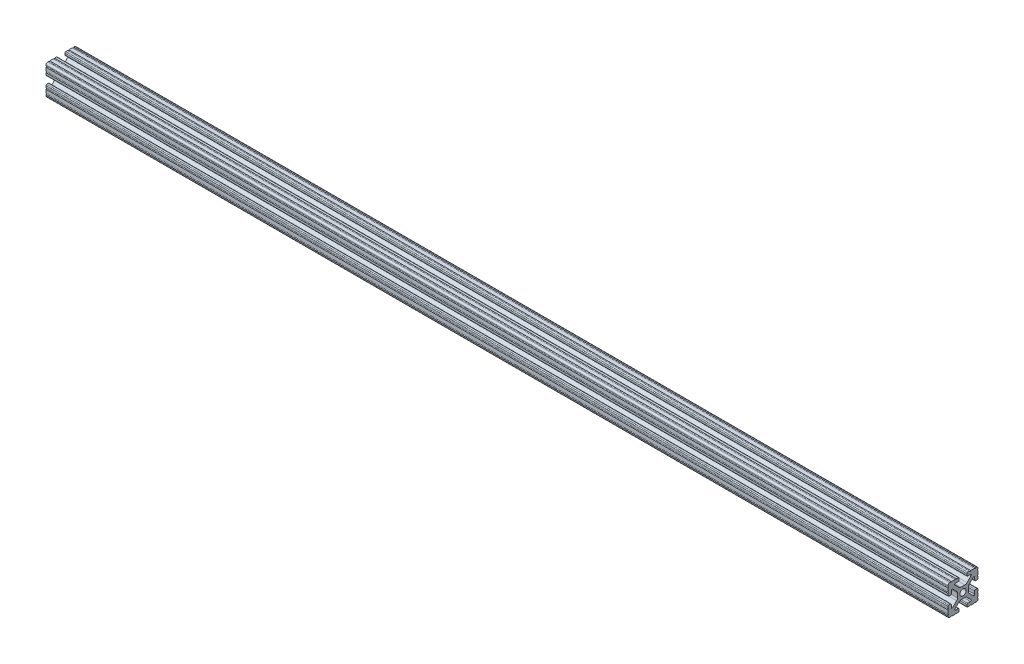
SolidWorks part; units mm, degrees
ref_plane "Front Plane" through (0, 0, 0) normal (0, 0, 1) x (1, 0, 0)
ref_plane "Top Plane" through (0, 0, 0) normal (0, 1, 0) x (1, 0, 0)
ref_plane "Right Plane" through (0, 0, 0) normal (1, 0, 0) x (0, 0, -1)
sketch "Sketch3"
sketch "Sketch2" plane through (0, 0, 0) normal (1, 0, 0) x (0, 0, -1)
  line L0 (16.1207, 7.3347) -> (19.544, 3.9114)
  line L1 (17.3256, 11.0651) -> (17.3256, 14.3349)
  line L2 (18.0653, 16.1207) -> (21.4886, 19.544)
  line L3 (22.598, 16.6362) -> (22.598, 19.0845)
  line L4 (24.7023, 15.9385) -> (23.2956, 15.9385)
  line L6 (2.1006, 25.4) -> (1.3474, 25.4)
  line L7 (16.6362, 2.802) -> (19.0845, 2.802)
  line L8 (0.6977, 15.9385) -> (2.1044, 15.9385)
  line L9 (2.802, 16.6362) -> (2.802, 19.0845)
  line L10 (0, 16.6362) -> (0, 18.2699)
  line L11 (8.0744, 11.0651) -> (8.0744, 14.3349)
  line L12 (7.3347, 16.1207) -> (3.9114, 19.544)
  line L13 (0, 19.2426) -> (0, 22.318)
  line L14 (0, 23.2994) -> (0, 24.0526)
  line L15 (6.1574, 25.4) -> (3.082, 25.4)
  line L16 (8.7638, 25.4) -> (7.1301, 25.4)
  line L17 (9.4615, 24.7023) -> (9.4615, 23.2956)
  line L18 (8.7638, 22.598) -> (6.3155, 22.598)
  line L19 (9.2793, 18.0653) -> (5.856, 21.4886)
  line L20 (14.3349, 17.3256) -> (11.0651, 17.3256)
  line L22 (25.4, 16.6362) -> (25.4, 18.2699)
  line L23 (25.4, 19.2426) -> (25.4, 22.318)
  line L24 (25.4, 23.2994) -> (25.4, 24.0526)
  line L25 (23.2994, 25.4) -> (24.0526, 25.4)
  line L26 (19.2426, 25.4) -> (22.318, 25.4)
  line L27 (16.6362, 25.4) -> (18.2699, 25.4)
  line L28 (15.9385, 24.7023) -> (15.9385, 23.2956)
  line L29 (16.6362, 22.598) -> (19.0845, 22.598)
  line L30 (16.1207, 18.0653) -> (19.544, 21.4886)
  line L31 (15.9385, 0.6977) -> (15.9385, 2.1044)
  line L32 (16.6362, 0) -> (18.2699, 0)
  line L33 (19.2426, 0) -> (22.318, 0)
  line L34 (23.2994, 0) -> (24.0526, 0)
  line L35 (25.4, 2.1006) -> (25.4, 1.3474)
  line L36 (25.4, 6.1574) -> (25.4, 3.082)
  line L37 (25.4, 8.7638) -> (25.4, 7.1301)
  line L38 (14.3349, 8.0744) -> (11.0651, 8.0744)
  line L39 (9.2793, 7.3347) -> (5.856, 3.9114)
  line L40 (8.7638, 2.802) -> (6.3155, 2.802)
  line L41 (9.4615, 0.6977) -> (9.4615, 2.1044)
  line L42 (8.7638, 0) -> (7.1301, 0)
  line L43 (6.1574, 0) -> (3.082, 0)
  line L44 (0, 2.1006) -> (0, 1.3474)
  line L45 (0, 6.1574) -> (0, 3.082)
  line L46 (7.3347, 9.2793) -> (3.9114, 5.856)
  line L47 (0, 8.7638) -> (0, 7.1301)
  line L48 (2.802, 8.7638) -> (2.802, 6.3155)
  line L49 (0.6977, 9.4615) -> (2.1044, 9.4615)
  line L50 (2.1006, 0) -> (1.3474, 0)
  line L51 (24.7023, 9.4615) -> (23.2956, 9.4615)
  line L52 (22.598, 8.7638) -> (22.598, 6.3155)
  line L53 (18.0653, 9.2793) -> (21.4886, 5.856)
  circle A0 centre (12.7, 12.7) radius 2.6035
  arc A1 (7.3347, 16.1207) -> (8.0744, 14.3349) centre (5.5489, 14.3349) cw
  arc A2 (2.802, 19.0845) -> (3.9114, 19.544) centre (3.4519, 19.0845) cw
  arc A3 (2.802, 16.6362) -> (2.1044, 15.9385) centre (2.1044, 16.6362) cw
  arc A4 (0, 16.6362) -> (0.6977, 15.9385) centre (0.6977, 16.6362) ccw
  arc A5 (-0.0204, 18.2642) -> (-0.0101, 19.2455) centre (-0.1467, 18.7562) ccw
  arc A6 (0, 22.318) -> (0, 23.2994) centre (-0.1315, 22.8087) ccw
  arc A7 (0, 24.0526) -> (1.3474, 25.4) centre (1.3474, 24.0526) cw
  arc A8 (3.082, 25.4) -> (2.1006, 25.4) centre (2.5913, 25.5315) cw
  arc A9 (7.1358, 25.4204) -> (6.1545, 25.4101) centre (6.6438, 25.5467) cw
  arc A10 (8.7638, 25.4) -> (9.4615, 24.7023) centre (8.7638, 24.7023) cw
  arc A11 (8.7638, 22.598) -> (9.4615, 23.2956) centre (8.7638, 23.2956) ccw
  arc A12 (6.3155, 22.598) -> (5.856, 21.4886) centre (6.3155, 21.9481) ccw
  arc A13 (9.2793, 18.0653) -> (11.0651, 17.3256) centre (11.0651, 19.8511) ccw
  arc A14 (18.0653, 16.1207) -> (17.3256, 14.3349) centre (19.8511, 14.3349) ccw
  arc A15 (22.598, 19.0845) -> (21.4886, 19.544) centre (21.9481, 19.0845) ccw
  arc A16 (22.598, 16.6362) -> (23.2956, 15.9385) centre (23.2956, 16.6362) ccw
  arc A17 (25.4, 16.6362) -> (24.7023, 15.9385) centre (24.7023, 16.6362) cw
  arc A18 (25.4204, 18.2642) -> (25.4101, 19.2455) centre (25.5467, 18.7562) cw
  arc A19 (25.4, 22.318) -> (25.4, 23.2994) centre (25.5315, 22.8087) cw
  arc A20 (25.4, 24.0526) -> (24.0526, 25.4) centre (24.0526, 24.0526) ccw
  arc A21 (22.318, 25.4) -> (23.2994, 25.4) centre (22.8087, 25.5315) ccw
  arc A22 (18.2642, 25.4204) -> (19.2455, 25.4101) centre (18.7562, 25.5467) ccw
  arc A23 (16.6362, 25.4) -> (15.9385, 24.7023) centre (16.6362, 24.7023) ccw
  arc A24 (16.6362, 22.598) -> (15.9385, 23.2956) centre (16.6362, 23.2956) cw
  arc A25 (19.0845, 22.598) -> (19.544, 21.4886) centre (19.0845, 21.9481) cw
  arc A26 (16.1207, 18.0653) -> (14.3349, 17.3256) centre (14.3349, 19.8511) cw
  arc A27 (16.1207, 7.3347) -> (14.3349, 8.0744) centre (14.3349, 5.5489) ccw
  arc A28 (19.0845, 2.802) -> (19.544, 3.9114) centre (19.0845, 3.4519) ccw
  arc A29 (16.6362, 2.802) -> (15.9385, 2.1044) centre (16.6362, 2.1044) ccw
  arc A30 (16.6362, 0) -> (15.9385, 0.6977) centre (16.6362, 0.6977) cw
  arc A31 (18.2642, -0.0204) -> (19.2455, -0.0101) centre (18.7562, -0.1467) cw
  arc A32 (22.318, 0) -> (23.2994, 0) centre (22.8087, -0.1315) cw
  arc A33 (25.4, 1.3474) -> (24.0526, 0) centre (24.0526, 1.3474) cw
  arc A34 (25.4, 3.082) -> (25.4, 2.1006) centre (25.5315, 2.5913) ccw
  arc A35 (25.4204, 7.1358) -> (25.4101, 6.1545) centre (25.5467, 6.6438) ccw
  arc A36 (25.4, 8.7638) -> (24.7023, 9.4615) centre (24.7023, 8.7638) ccw
  arc A37 (22.598, 8.7638) -> (23.2956, 9.4615) centre (23.2956, 8.7638) cw
  arc A38 (22.598, 6.3155) -> (21.4886, 5.856) centre (21.9481, 6.3155) cw
  arc A39 (18.0653, 9.2793) -> (17.3256, 11.0651) centre (19.8511, 11.0651) cw
  arc A40 (9.2793, 7.3347) -> (11.0651, 8.0744) centre (11.0651, 5.5489) cw
  arc A41 (6.3155, 2.802) -> (5.856, 3.9114) centre (6.3155, 3.4519) cw
  arc A42 (8.7638, 2.802) -> (9.4615, 2.1044) centre (8.7638, 2.1044) cw
  arc A43 (8.7638, 0) -> (9.4615, 0.6977) centre (8.7638, 0.6977) ccw
  arc A44 (7.1358, -0.0204) -> (6.1545, -0.0101) centre (6.6438, -0.1467) ccw
  arc A45 (3.082, 0) -> (2.1006, 0) centre (2.5913, -0.1315) ccw
  arc A46 (0, 1.3474) -> (1.3474, 0) centre (1.3474, 1.3474) ccw
  arc A47 (0, 3.082) -> (0, 2.1006) centre (-0.1315, 2.5913) cw
  arc A48 (-0.0204, 7.1358) -> (-0.0101, 6.1545) centre (-0.1467, 6.6438) cw
  arc A49 (0, 8.7638) -> (0.6977, 9.4615) centre (0.6977, 8.7638) cw
  arc A50 (2.802, 8.7638) -> (2.1044, 9.4615) centre (2.1044, 8.7638) ccw
  arc A51 (2.802, 6.3155) -> (3.9114, 5.856) centre (3.4519, 6.3155) ccw
  arc A52 (7.3347, 9.2793) -> (8.0744, 11.0651) centre (5.5489, 11.0651) ccw
  point P100 (12.7, 17.3256)
  point P181 (8.0744, 12.7)
  point P182 (17.3256, 12.7)
extrude "Boss-Extrude1" add sketch "Sketch2" along normal blind 762 contours A52 L46 A51 L48 A50 L49 A49 L47 A48 L45 A47 L44 A46 L50 A45 L43 A44 L42 A43 L41 A42 L40 A41 L39 A40 L38 A27 L0 A28 L7 A29 L31 A30 L32 A31 L33 A32 L34 A33 L35 A34 L36 A35 L37 A36 L51 A37 L52 A38 L53 A39
move or copy body "Body-Move/Copy1" bodies to move or copy 102 copy no translate (-150.0587, 28.7597, 59.645)
sketch "Sketch4" plane through (0, 0, 0) normal (0, 0, 1) x (1, 0, 0)
  line L0 (611.9413, 54.1597) -> (-150.0587, 54.1597) construction
  line L1 (-78.6761, 54.1597) -> (-106.0407, -11.9043)
  line L2 (378.5239, 54.1597) -> (405.8885, -11.9043)
  line L3 (405.8885, -11.9043) -> (480.3446, -42.745)
  line L4 (480.3446, -42.745) -> (535.2221, 89.7411)
  line L5 (535.2221, 89.7411) -> (378.5239, 89.7411)
  line L6 (378.5239, 89.7411) -> (378.5239, 54.1597)
  line L7 (-78.6761, 54.1597) -> (-78.6761, 92.6727)
  line L8 (-78.6761, 92.6727) -> (-197.9311, 43.2757)
  line L9 (-197.9311, 43.2757) -> (-164.965, -36.3115)
  line L10 (-164.965, -36.3115) -> (-106.0407, -11.9043)
  dimension "D1" = 67.5
  dimension "D2" = 67.5
sketch "Sketch5" plane through (0, 0, 59.645) normal (0, 0, 1) x (1, 0, 0)
  line L0 (-150.0587, 54.1597) -> (-150.0587, 28.7597)
  line L1 (-150.0587, 28.7597) -> (-124.6587, 28.7597)
  line L2 (611.9413, 28.7597) -> (-150.0587, 28.7597) construction
  line L3 (611.9413, 54.1597) -> (-150.0587, 54.1597) construction
  line L4 (611.9413, 48.0023) -> (611.9413, 51.0777) construction
  line L5 (611.9413, 54.1597) -> (-150.0587, 54.1597) construction
  arc A0 (-150.0587, 54.1597) -> (-124.6587, 28.7597) centre (-124.6587, 54.1597) ccw
  circle A1 centre (-137.3587, 41.4597) radius 3.3858
  circle A2 centre (599.2413, 41.4597) radius 3.3858
  point P17 (611.9413, 49.54)
  line M2 (-150.0587, 51.0777) -> (-150.0587, 48.0023)
  line M3 (-150.0587, 48.0023) -> (611.9413, 48.0023)
  line M5 (611.9413, 51.0777) -> (-150.0587, 51.0777)
  dimension "D4" = 6.7716
  dimension "D7" = 6.7716
  dimension "D1" = 0
  dimension "D2" = 25.4
  dimension "D3" = 25.4
  dimension "D5" = 12.7
  dimension "D6" = 12.7
  dimension "D8" = 12.7
  dimension "D9" = 12.7
extrude "Cut-Extrude1" [suppressed] cut sketch "Sketch5" against normal through all contours A0 L0 L1 M3 | A0 M5 M2 M3 | A0 L0 M5 | A1 | A2
